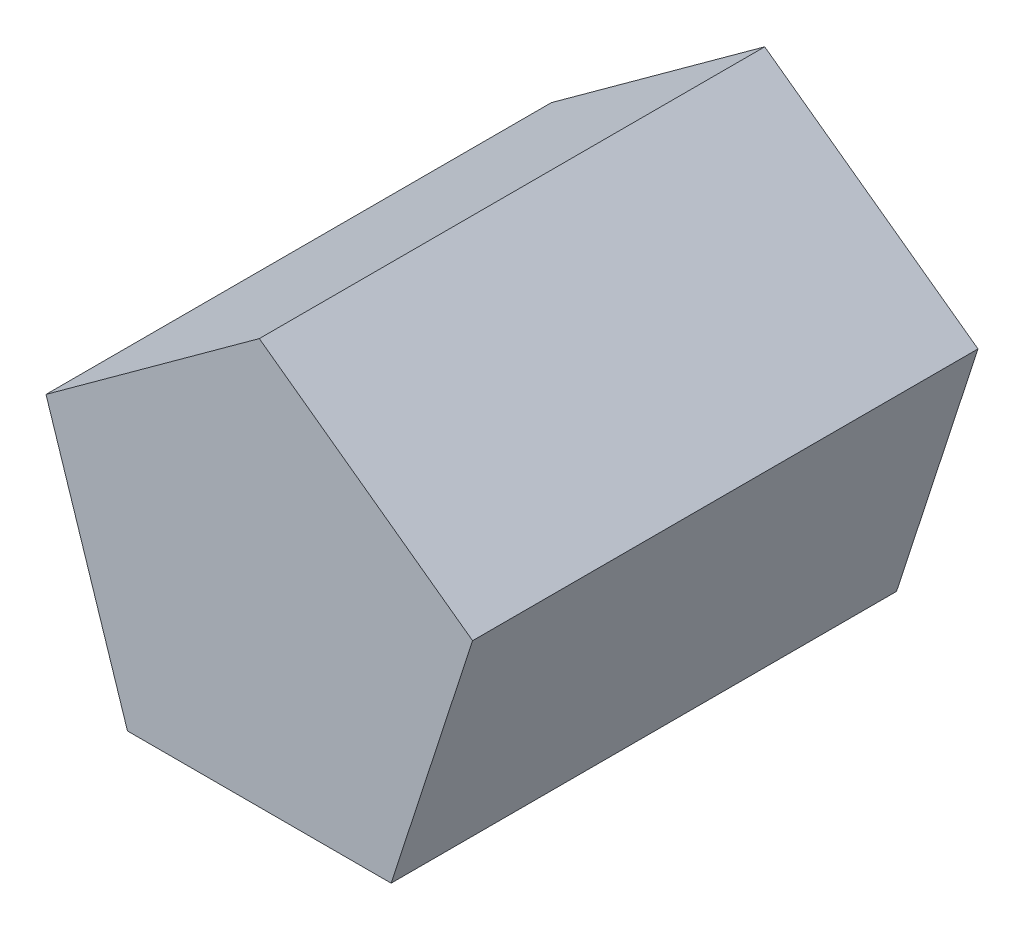
SolidWorks part; units mm, degrees
ref_plane "Piano frontale" through (0, 0, 0) normal (0, 0, 1) x (1, 0, 0)
ref_plane "Piano superiore" through (0, 0, 0) normal (0, 1, 0) x (1, 0, 0)
ref_plane "Piano destro" through (0, 0, 0) normal (1, 0, 0) x (0, 0, -1)
sketch "Schizzo1" plane through (0, 0, 0) normal (0, 0, 1) x (1, 0, 0)
  line L1 (41.7328, -57.4402) -> (67.525, 21.9402)
  line L2 (67.525, 21.9402) -> (0, 71)
  line L3 (0, 71) -> (-67.525, 21.9402)
  line L4 (-67.525, 21.9402) -> (-41.7328, -57.4402)
  line L5 (-41.7328, -57.4402) -> (41.7328, -57.4402)
  circle A0 centre (0, 0) radius 57.4402 construction
  dimension "D1" = 71
extrude "Estrusione-Estrusione1" add sketch "Schizzo1" along normal blind 160
